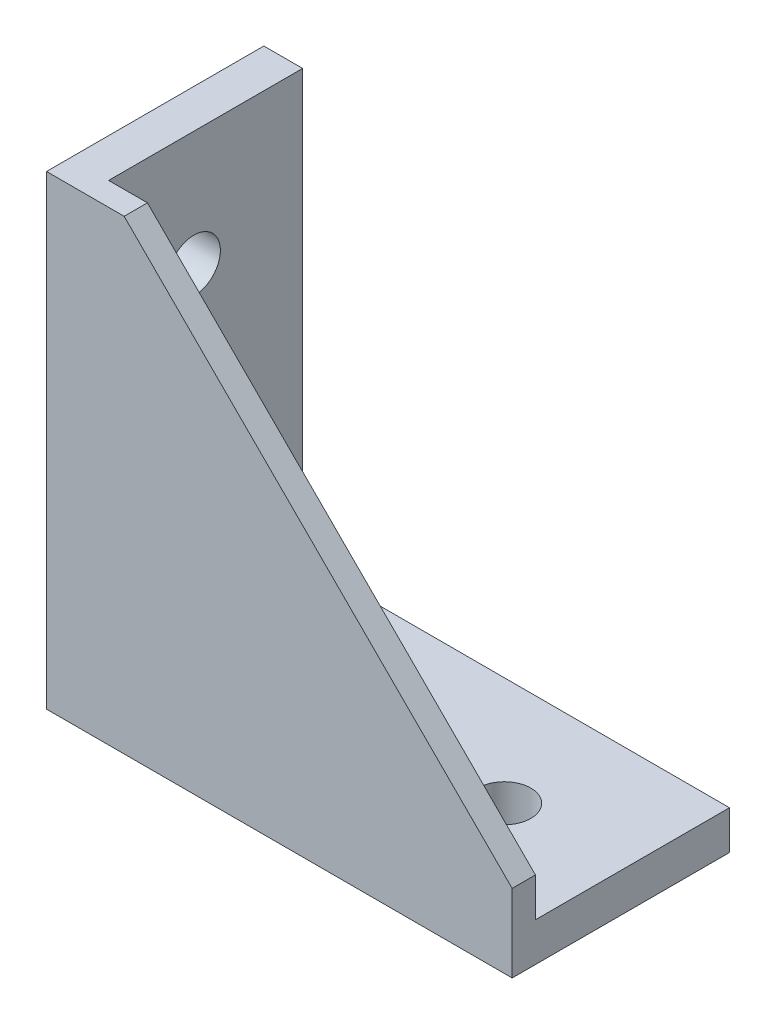
SolidWorks part; units mm, degrees
material "Алюминиевый сплав"
ref_plane "Спереди" through (0, 0, 0) normal (0, 0, 1) x (1, 0, 0)
ref_plane "Сверху" through (0, 0, 0) normal (0, 1, 0) x (1, 0, 0)
ref_plane "Справа" through (0, 0, 0) normal (1, 0, 0) x (0, 0, -1)
sketch "Эскиз1" plane through (0, 0, 0) normal (0, 0, 1) x (1, 0, 0)
  line L0 (0, 60) -> (0, 0)
  line L1 (0, 0) -> (60, 0)
  line L2 (60, 0) -> (60, 5)
  line L4 (5, 60) -> (0, 60)
  line L5 (5, 60) -> (5, 5)
  line L6 (5, 5) -> (60, 5)
  dimension "D1" = 60
  dimension "D2" = 5
extrude "Бобышка-Вытянуть1" add sketch "Эскиз1" along normal mid plane 28
sketch "Эскиз2" plane through (0, 0, 14) normal (0, 0, 1) x (1, 0, 0)
  line L1 (60, 5) -> (5, 5)
  line L2 (5, 5) -> (5, 60)
  line L3 (60, 0) -> (60, 5) construction
  line L4 (5, 60) -> (10, 60)
  line L5 (10, 60) -> (60, 10)
  line L6 (60, 10) -> (60, 5)
extrude "Бобышка-Вытянуть2" add sketch "Эскиз2" against normal blind 3
sketch "Эскиз3" plane through (0, 5, 0) normal (0, 1, 0) x (1, 0, 0)
  line L0 (18, 0) -> (31.5, 0) construction
  line L1 (18, 3.4) -> (31.5, 3.4)
  line L2 (18, -3.4) -> (31.5, -3.4)
  line L3 (0, -14) -> (0, 14) construction
  arc A0 (18, 3.4) -> (18, -3.4) centre (18, 0) ccw
  arc A1 (31.5, -3.4) -> (31.5, 3.4) centre (31.5, 0) ccw
  circle A2 centre (45, 0) radius 3.4
  point P2 (24.75, 0)
  dimension "D2" = 3.4
  dimension "D3" = 18
  dimension "D4" = 13.5
  dimension "D1" = 13.5
extrude "Вырез-Вытянуть1" cut sketch "Эскиз3" against normal through all
sketch "Эскиз4" plane through (0, 0, 0) normal (0, -1, 0) x (1, 0, 0)
  line L0 (0, 14) -> (0, -14) construction
  line L1 (3, -4) -> (5.5, -4)
  line L2 (3, -4) -> (3, 4)
  line L3 (3, 4) -> (5.5, 4)
  line L4 (5.5, -4) -> (5.5, 4)
  line L5 (3, -4) -> (5.5, 4) construction
  line L6 (3, 4) -> (5.5, -4) construction
  line L7 (54.5, -4) -> (57, -4)
  line L8 (54.5, -4) -> (54.5, 4)
  line L9 (54.5, 4) -> (57, 4)
  line L10 (57, -4) -> (57, 4)
  line L11 (54.5, -4) -> (57, 4) construction
  line L12 (54.5, 4) -> (57, -4) construction
  line L13 (60, 14) -> (60, -14) construction
  point P0 (4.25, 0)
  point P5 (55.75, 0)
  dimension "D1" = 3
  dimension "D2" = 2.5
  dimension "D3" = 8
  dimension "D4" = 3
extrude "Бобышка-Вытянуть3" add sketch "Эскиз4" along normal blind 2.5
ref_plane "Плоскость1" through (0, 0, 0) normal (-0.7071, 0.7071, 0) x (0.7071, 0.7071, 0)
mirror "Зеркальное отражение3" about plane through (0, 0, 0) normal (-0.7071, 0.7071, 0) of "Бобышка-Вытянуть3", "Вырез-Вытянуть1"
